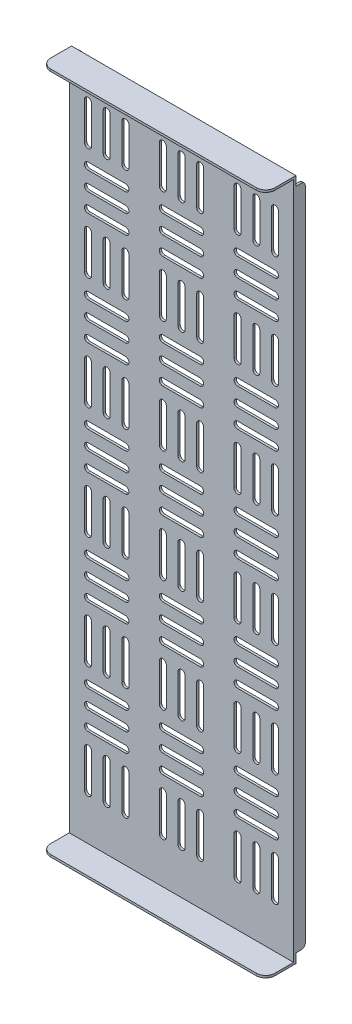
SolidWorks part; units mm, degrees
ref_plane "Front Plane" through (0, 0, 0) normal (0, 0, 1) x (1, 0, 0)
ref_plane "Top Plane" through (0, 0, 0) normal (0, 1, 0) x (1, 0, 0)
ref_plane "Right Plane" through (0, 0, 0) normal (1, 0, 0) x (0, 0, -1)
sketch "Sketch1" plane through (0, 0, 0) normal (0, 0, 1) x (1, 0, 0)
  line L0 (12.7, 438.15) -> (12.7, 412.75) construction
  line L1 (0, 0) -> (152.4, 0)
  line L2 (0, 0) -> (0, 463.55)
  line L3 (0, 463.55) -> (152.4, 463.55)
  line L4 (152.4, 0) -> (152.4, 463.55)
  line L5 (15.0812, 438.15) -> (15.0813, 412.75)
  line L6 (10.3188, 438.15) -> (10.3188, 412.75)
  line L7 (25.4, 438.15) -> (25.4, 412.75) construction
  line L8 (27.7812, 438.15) -> (27.7812, 412.75)
  line L9 (23.0188, 438.15) -> (23.0188, 412.75)
  line L10 (38.1, 438.15) -> (38.1, 412.75) construction
  line L11 (40.4812, 438.15) -> (40.4813, 412.75)
  line L12 (35.7188, 438.15) -> (35.7188, 412.75)
  line L13 (63.5, 438.15) -> (63.5, 412.75) construction
  line L14 (65.8813, 438.15) -> (65.8813, 412.75)
  line L15 (61.1187, 438.15) -> (61.1187, 412.75)
  line L16 (76.2, 438.15) -> (76.2, 412.75) construction
  line L17 (78.5812, 438.15) -> (78.5812, 412.75)
  line L18 (73.8188, 438.15) -> (73.8188, 412.75)
  line L19 (88.9, 438.15) -> (88.9, 412.75) construction
  line L20 (91.2812, 438.15) -> (91.2813, 412.75)
  line L21 (86.5188, 438.15) -> (86.5188, 412.75)
  line L22 (114.3, 438.15) -> (114.3, 412.75) construction
  line L23 (116.6813, 438.15) -> (116.6813, 412.75)
  line L24 (111.9188, 438.15) -> (111.9188, 412.75)
  line L25 (127, 438.15) -> (127, 412.75) construction
  line L26 (129.3812, 438.15) -> (129.3812, 412.75)
  line L27 (124.6188, 438.15) -> (124.6188, 412.75)
  line L28 (139.7, 438.15) -> (139.7, 412.75) construction
  line L29 (142.0812, 438.15) -> (142.0812, 412.75)
  line L30 (137.3187, 438.15) -> (137.3187, 412.75)
  line L31 (12.7, 400.05) -> (38.1, 400.05) construction
  line L32 (12.7, 402.4313) -> (38.1, 402.4313)
  line L33 (12.7, 397.6687) -> (38.1, 397.6687)
  line L34 (12.7, 387.35) -> (38.1, 387.35) construction
  line L35 (12.7, 389.7313) -> (38.1, 389.7313)
  line L36 (12.7, 384.9688) -> (38.1, 384.9688)
  line L37 (12.7, 374.65) -> (38.1, 374.65) construction
  line L38 (12.7, 377.0313) -> (38.1, 377.0313)
  line L39 (12.7, 372.2688) -> (38.1, 372.2688)
  line L40 (63.5, 400.05) -> (88.9, 400.05) construction
  line L41 (63.5, 402.4313) -> (88.9, 402.4313)
  line L42 (63.5, 397.6687) -> (88.9, 397.6687)
  line L43 (63.5, 387.35) -> (88.9, 387.35) construction
  line L44 (63.5, 389.7313) -> (88.9, 389.7313)
  line L45 (63.5, 384.9688) -> (88.9, 384.9688)
  line L46 (63.5, 374.65) -> (88.9, 374.65) construction
  line L47 (63.5, 377.0313) -> (88.9, 377.0313)
  line L48 (63.5, 372.2688) -> (88.9, 372.2688)
  line L49 (114.3, 400.05) -> (139.7, 400.05) construction
  line L50 (114.3, 402.4313) -> (139.7, 402.4313)
  line L51 (114.3, 397.6687) -> (139.7, 397.6687)
  line L52 (114.3, 387.35) -> (139.7, 387.35) construction
  line L53 (114.3, 389.7313) -> (139.7, 389.7313)
  line L54 (114.3, 384.9688) -> (139.7, 384.9688)
  line L55 (114.3, 374.65) -> (139.7, 374.65) construction
  line L56 (114.3, 377.0313) -> (139.7, 377.0313)
  line L57 (114.3, 372.2688) -> (139.7, 372.2688)
  line L58 (12.7, 361.95) -> (12.7, 336.55) construction
  line L59 (15.0813, 361.95) -> (15.0813, 336.55)
  line L60 (10.3188, 361.95) -> (10.3188, 336.55)
  line L61 (25.4, 361.95) -> (25.4, 336.55) construction
  line L62 (27.7813, 361.95) -> (27.7813, 336.55)
  line L63 (23.0188, 361.95) -> (23.0188, 336.55)
  line L64 (38.1, 361.95) -> (38.1, 336.55) construction
  line L65 (40.4813, 361.95) -> (40.4813, 336.55)
  line L66 (35.7188, 361.95) -> (35.7188, 336.55)
  line L67 (63.5, 361.95) -> (63.5, 336.55) construction
  line L68 (65.8813, 361.95) -> (65.8813, 336.55)
  line L69 (61.1188, 361.95) -> (61.1188, 336.55)
  line L70 (76.2, 361.95) -> (76.2, 336.55) construction
  line L71 (78.5813, 361.95) -> (78.5813, 336.55)
  line L72 (73.8188, 361.95) -> (73.8188, 336.55)
  line L73 (88.9, 361.95) -> (88.9, 336.55) construction
  line L74 (91.2813, 361.95) -> (91.2813, 336.55)
  line L75 (86.5188, 361.95) -> (86.5188, 336.55)
  line L76 (114.3, 361.95) -> (114.3, 336.55) construction
  line L77 (116.6813, 361.95) -> (116.6813, 336.55)
  line L78 (111.9188, 361.95) -> (111.9188, 336.55)
  line L79 (127, 361.95) -> (127, 336.55) construction
  line L80 (129.3813, 361.95) -> (129.3813, 336.55)
  line L81 (124.6188, 361.95) -> (124.6188, 336.55)
  line L82 (139.7, 361.95) -> (139.7, 336.55) construction
  line L83 (142.0813, 361.95) -> (142.0813, 336.55)
  line L84 (137.3188, 361.95) -> (137.3188, 336.55)
  line L85 (12.7, 323.85) -> (38.1, 323.85) construction
  line L86 (12.7, 326.2313) -> (38.1, 326.2313)
  line L87 (12.7, 321.4688) -> (38.1, 321.4688)
  line L88 (12.7, 311.15) -> (38.1, 311.15) construction
  line L89 (12.7, 313.5313) -> (38.1, 313.5313)
  line L90 (12.7, 308.7688) -> (38.1, 308.7688)
  line L91 (12.7, 298.45) -> (38.1, 298.45) construction
  line L92 (12.7, 300.8313) -> (38.1, 300.8313)
  line L93 (12.7, 296.0688) -> (38.1, 296.0688)
  line L94 (63.5, 323.85) -> (88.9, 323.85) construction
  line L95 (63.5, 326.2313) -> (88.9, 326.2313)
  line L96 (63.5, 321.4688) -> (88.9, 321.4688)
  line L97 (63.5, 311.15) -> (88.9, 311.15) construction
  line L98 (63.5, 313.5313) -> (88.9, 313.5313)
  line L99 (63.5, 308.7688) -> (88.9, 308.7688)
  line L100 (63.5, 298.45) -> (88.9, 298.45) construction
  line L101 (63.5, 300.8313) -> (88.9, 300.8313)
  line L102 (63.5, 296.0688) -> (88.9, 296.0688)
  line L103 (114.3, 323.85) -> (139.7, 323.85) construction
  line L104 (114.3, 326.2313) -> (139.7, 326.2313)
  line L105 (114.3, 321.4688) -> (139.7, 321.4688)
  line L106 (114.3, 311.15) -> (139.7, 311.15) construction
  line L107 (114.3, 313.5313) -> (139.7, 313.5313)
  line L108 (114.3, 308.7688) -> (139.7, 308.7688)
  line L109 (114.3, 298.45) -> (139.7, 298.45) construction
  line L110 (114.3, 300.8313) -> (139.7, 300.8313)
  line L111 (114.3, 296.0688) -> (139.7, 296.0688)
  line L112 (12.7, 285.75) -> (12.7, 260.35) construction
  line L113 (15.0813, 285.75) -> (15.0813, 260.35)
  line L114 (10.3188, 285.75) -> (10.3188, 260.35)
  line L115 (25.4, 285.75) -> (25.4, 260.35) construction
  line L116 (27.7813, 285.75) -> (27.7813, 260.35)
  line L117 (23.0188, 285.75) -> (23.0188, 260.35)
  line L118 (38.1, 285.75) -> (38.1, 260.35) construction
  line L119 (40.4813, 285.75) -> (40.4813, 260.35)
  line L120 (35.7188, 285.75) -> (35.7188, 260.35)
  line L121 (63.5, 285.75) -> (63.5, 260.35) construction
  line L122 (65.8813, 285.75) -> (65.8813, 260.35)
  line L123 (61.1188, 285.75) -> (61.1188, 260.35)
  line L124 (76.2, 285.75) -> (76.2, 260.35) construction
  line L125 (78.5813, 285.75) -> (78.5813, 260.35)
  line L126 (73.8188, 285.75) -> (73.8188, 260.35)
  line L127 (88.9, 285.75) -> (88.9, 260.35) construction
  line L128 (91.2813, 285.75) -> (91.2813, 260.35)
  line L129 (86.5188, 285.75) -> (86.5188, 260.35)
  line L130 (114.3, 285.75) -> (114.3, 260.35) construction
  line L131 (116.6813, 285.75) -> (116.6813, 260.35)
  line L132 (111.9188, 285.75) -> (111.9188, 260.35)
  line L133 (127, 285.75) -> (127, 260.35) construction
  line L134 (129.3813, 285.75) -> (129.3813, 260.35)
  line L135 (124.6188, 285.75) -> (124.6188, 260.35)
  line L136 (139.7, 285.75) -> (139.7, 260.35) construction
  line L137 (142.0813, 285.75) -> (142.0813, 260.35)
  line L138 (137.3188, 285.75) -> (137.3188, 260.35)
  line L139 (12.7, 247.65) -> (38.1, 247.65) construction
  line L140 (12.7, 250.0313) -> (38.1, 250.0313)
  line L141 (12.7, 245.2688) -> (38.1, 245.2688)
  line L142 (12.7, 234.95) -> (38.1, 234.95) construction
  line L143 (12.7, 237.3313) -> (38.1, 237.3313)
  line L144 (12.7, 232.5688) -> (38.1, 232.5688)
  line L145 (12.7, 222.25) -> (38.1, 222.25) construction
  line L146 (12.7, 224.6313) -> (38.1, 224.6313)
  line L147 (12.7, 219.8688) -> (38.1, 219.8688)
  line L148 (63.5, 247.65) -> (88.9, 247.65) construction
  line L149 (63.5, 250.0313) -> (88.9, 250.0313)
  line L150 (63.5, 245.2688) -> (88.9, 245.2688)
  line L151 (63.5, 234.95) -> (88.9, 234.95) construction
  line L152 (63.5, 237.3313) -> (88.9, 237.3313)
  line L153 (63.5, 232.5688) -> (88.9, 232.5688)
  line L154 (63.5, 222.25) -> (88.9, 222.25) construction
  line L155 (63.5, 224.6313) -> (88.9, 224.6313)
  line L156 (63.5, 219.8688) -> (88.9, 219.8688)
  line L157 (114.3, 247.65) -> (139.7, 247.65) construction
  line L158 (114.3, 250.0313) -> (139.7, 250.0313)
  line L159 (114.3, 245.2688) -> (139.7, 245.2688)
  line L160 (114.3, 234.95) -> (139.7, 234.95) construction
  line L161 (114.3, 237.3313) -> (139.7, 237.3313)
  line L162 (114.3, 232.5688) -> (139.7, 232.5688)
  line L163 (114.3, 222.25) -> (139.7, 222.25) construction
  line L164 (114.3, 224.6313) -> (139.7, 224.6313)
  line L165 (114.3, 219.8688) -> (139.7, 219.8688)
  line L166 (12.7, 209.55) -> (12.7, 184.15) construction
  line L167 (15.0813, 209.55) -> (15.0813, 184.15)
  line L168 (10.3188, 209.55) -> (10.3188, 184.15)
  line L169 (25.4, 209.55) -> (25.4, 184.15) construction
  line L170 (27.7813, 209.55) -> (27.7813, 184.15)
  line L171 (23.0188, 209.55) -> (23.0188, 184.15)
  line L172 (38.1, 209.55) -> (38.1, 184.15) construction
  line L173 (40.4813, 209.55) -> (40.4813, 184.15)
  line L174 (35.7188, 209.55) -> (35.7188, 184.15)
  line L175 (63.5, 209.55) -> (63.5, 184.15) construction
  line L176 (65.8813, 209.55) -> (65.8813, 184.15)
  line L177 (61.1188, 209.55) -> (61.1188, 184.15)
  line L178 (76.2, 209.55) -> (76.2, 184.15) construction
  line L179 (78.5813, 209.55) -> (78.5813, 184.15)
  line L180 (73.8188, 209.55) -> (73.8188, 184.15)
  line L181 (88.9, 209.55) -> (88.9, 184.15) construction
  line L182 (91.2813, 209.55) -> (91.2813, 184.15)
  line L183 (86.5188, 209.55) -> (86.5188, 184.15)
  line L184 (114.3, 209.55) -> (114.3, 184.15) construction
  line L185 (116.6813, 209.55) -> (116.6813, 184.15)
  line L186 (111.9188, 209.55) -> (111.9188, 184.15)
  line L187 (127, 209.55) -> (127, 184.15) construction
  line L188 (129.3813, 209.55) -> (129.3813, 184.15)
  line L189 (124.6188, 209.55) -> (124.6188, 184.15)
  line L190 (139.7, 209.55) -> (139.7, 184.15) construction
  line L191 (142.0813, 209.55) -> (142.0813, 184.15)
  line L192 (137.3188, 209.55) -> (137.3188, 184.15)
  line L193 (12.7, 171.45) -> (38.1, 171.45) construction
  line L194 (12.7, 173.8312) -> (38.1, 173.8312)
  line L195 (12.7, 169.0687) -> (38.1, 169.0687)
  line L196 (12.7, 158.75) -> (38.1, 158.75) construction
  line L197 (12.7, 161.1312) -> (38.1, 161.1312)
  line L198 (12.7, 156.3688) -> (38.1, 156.3688)
  line L199 (12.7, 146.05) -> (38.1, 146.05) construction
  line L200 (12.7, 148.4313) -> (38.1, 148.4313)
  line L201 (12.7, 143.6688) -> (38.1, 143.6688)
  line L202 (63.5, 171.45) -> (88.9, 171.45) construction
  line L203 (63.5, 173.8312) -> (88.9, 173.8312)
  line L204 (63.5, 169.0687) -> (88.9, 169.0687)
  line L205 (63.5, 158.75) -> (88.9, 158.75) construction
  line L206 (63.5, 161.1312) -> (88.9, 161.1312)
  line L207 (63.5, 156.3688) -> (88.9, 156.3688)
  line L208 (63.5, 146.05) -> (88.9, 146.05) construction
  line L209 (63.5, 148.4313) -> (88.9, 148.4313)
  line L210 (63.5, 143.6688) -> (88.9, 143.6688)
  line L211 (114.3, 171.45) -> (139.7, 171.45) construction
  line L212 (114.3, 173.8312) -> (139.7, 173.8312)
  line L213 (114.3, 169.0687) -> (139.7, 169.0687)
  line L214 (114.3, 158.75) -> (139.7, 158.75) construction
  line L215 (114.3, 161.1312) -> (139.7, 161.1312)
  line L216 (114.3, 156.3688) -> (139.7, 156.3688)
  line L217 (114.3, 146.05) -> (139.7, 146.05) construction
  line L218 (114.3, 148.4313) -> (139.7, 148.4313)
  line L219 (114.3, 143.6688) -> (139.7, 143.6688)
  line L220 (12.7, 133.35) -> (12.7, 107.95) construction
  line L221 (15.0813, 133.35) -> (15.0813, 107.95)
  line L222 (10.3187, 133.35) -> (10.3187, 107.95)
  line L223 (25.4, 133.35) -> (25.4, 107.95) construction
  line L224 (27.7813, 133.35) -> (27.7813, 107.95)
  line L225 (23.0187, 133.35) -> (23.0187, 107.95)
  line L226 (38.1, 133.35) -> (38.1, 107.95) construction
  line L227 (40.4813, 133.35) -> (40.4813, 107.95)
  line L228 (35.7187, 133.35) -> (35.7187, 107.95)
  line L229 (63.5, 133.35) -> (63.5, 107.95) construction
  line L230 (65.8813, 133.35) -> (65.8813, 107.95)
  line L231 (61.1187, 133.35) -> (61.1187, 107.95)
  line L232 (76.2, 133.35) -> (76.2, 107.95) construction
  line L233 (78.5813, 133.35) -> (78.5813, 107.95)
  line L234 (73.8187, 133.35) -> (73.8187, 107.95)
  line L235 (88.9, 133.35) -> (88.9, 107.95) construction
  line L236 (91.2813, 133.35) -> (91.2813, 107.95)
  line L237 (86.5187, 133.35) -> (86.5187, 107.95)
  line L238 (114.3, 133.35) -> (114.3, 107.95) construction
  line L239 (116.6813, 133.35) -> (116.6813, 107.95)
  line L240 (111.9187, 133.35) -> (111.9187, 107.95)
  line L241 (127, 133.35) -> (127, 107.95) construction
  line L242 (129.3813, 133.35) -> (129.3813, 107.95)
  line L243 (124.6187, 133.35) -> (124.6187, 107.95)
  line L244 (139.7, 133.35) -> (139.7, 107.95) construction
  line L245 (142.0813, 133.35) -> (142.0813, 107.95)
  line L246 (137.3187, 133.35) -> (137.3187, 107.95)
  line L247 (12.7, 95.25) -> (38.1, 95.25) construction
  line L248 (12.7, 97.6313) -> (38.1, 97.6313)
  line L249 (12.7, 92.8688) -> (38.1, 92.8688)
  line L250 (12.7, 82.55) -> (38.1, 82.55) construction
  line L251 (12.7, 84.9313) -> (38.1, 84.9313)
  line L252 (12.7, 80.1688) -> (38.1, 80.1688)
  line L253 (12.7, 69.85) -> (38.1, 69.85) construction
  line L254 (12.7, 72.2313) -> (38.1, 72.2313)
  line L255 (12.7, 67.4688) -> (38.1, 67.4688)
  line L256 (63.5, 95.25) -> (88.9, 95.25) construction
  line L257 (63.5, 97.6313) -> (88.9, 97.6313)
  line L258 (63.5, 92.8688) -> (88.9, 92.8688)
  line L259 (63.5, 82.55) -> (88.9, 82.55) construction
  line L260 (63.5, 84.9313) -> (88.9, 84.9313)
  line L261 (63.5, 80.1688) -> (88.9, 80.1688)
  line L262 (63.5, 69.85) -> (88.9, 69.85) construction
  line L263 (63.5, 72.2313) -> (88.9, 72.2313)
  line L264 (63.5, 67.4688) -> (88.9, 67.4688)
  line L265 (114.3, 95.25) -> (139.7, 95.25) construction
  line L266 (114.3, 97.6313) -> (139.7, 97.6313)
  line L267 (114.3, 92.8688) -> (139.7, 92.8688)
  line L268 (114.3, 82.55) -> (139.7, 82.55) construction
  line L269 (114.3, 84.9313) -> (139.7, 84.9313)
  line L270 (114.3, 80.1688) -> (139.7, 80.1688)
  line L271 (114.3, 69.85) -> (139.7, 69.85) construction
  line L272 (114.3, 72.2313) -> (139.7, 72.2313)
  line L273 (114.3, 67.4688) -> (139.7, 67.4688)
  line L274 (12.7, 57.15) -> (12.7, 31.75) construction
  line L275 (15.0813, 57.15) -> (15.0813, 31.75)
  line L276 (10.3187, 57.15) -> (10.3187, 31.75)
  line L277 (25.4, 57.15) -> (25.4, 31.75) construction
  line L278 (27.7813, 57.15) -> (27.7813, 31.75)
  line L279 (23.0187, 57.15) -> (23.0187, 31.75)
  line L280 (38.1, 57.15) -> (38.1, 31.75) construction
  line L281 (40.4813, 57.15) -> (40.4813, 31.75)
  line L282 (35.7187, 57.15) -> (35.7187, 31.75)
  line L283 (63.5, 57.15) -> (63.5, 31.75) construction
  line L284 (65.8813, 57.15) -> (65.8813, 31.75)
  line L285 (61.1187, 57.15) -> (61.1187, 31.75)
  line L286 (76.2, 57.15) -> (76.2, 31.75) construction
  line L287 (78.5813, 57.15) -> (78.5813, 31.75)
  line L288 (73.8187, 57.15) -> (73.8187, 31.75)
  line L289 (88.9, 57.15) -> (88.9, 31.75) construction
  line L290 (91.2813, 57.15) -> (91.2813, 31.75)
  line L291 (86.5187, 57.15) -> (86.5187, 31.75)
  line L292 (114.3, 57.15) -> (114.3, 31.75) construction
  line L293 (116.6813, 57.15) -> (116.6813, 31.75)
  line L294 (111.9187, 57.15) -> (111.9187, 31.75)
  line L295 (127, 57.15) -> (127, 31.75) construction
  line L296 (129.3813, 57.15) -> (129.3813, 31.75)
  line L297 (124.6187, 57.15) -> (124.6187, 31.75)
  line L298 (139.7, 57.15) -> (139.7, 31.75) construction
  line L299 (142.0813, 57.15) -> (142.0813, 31.75)
  line L300 (137.3187, 57.15) -> (137.3187, 31.75)
  line L331 (12.7, 6.35) -> (38.1, 6.35) construction
  line L332 (12.7, 8.7313) -> (38.1, 8.7313)
  line L333 (12.7, 3.9688) -> (38.1, 3.9688)
  line L334 (12.7, -6.35) -> (38.1, -6.35) construction
  line L335 (12.7, -3.9687) -> (38.1, -3.9687)
  line L336 (12.7, -8.7312) -> (38.1, -8.7312)
  line L337 (63.5, 19.05) -> (88.9, 19.05) construction
  line L338 (63.5, 21.4313) -> (88.9, 21.4313)
  line L339 (63.5, 16.6688) -> (88.9, 16.6688)
  line L340 (63.5, 6.35) -> (88.9, 6.35) construction
  line L341 (63.5, 8.7313) -> (88.9, 8.7313)
  line L342 (63.5, 3.9688) -> (88.9, 3.9688)
  line L343 (63.5, -6.35) -> (88.9, -6.35) construction
  line L344 (63.5, -3.9687) -> (88.9, -3.9687)
  line L345 (63.5, -8.7312) -> (88.9, -8.7312)
  line L346 (114.3, 19.05) -> (139.7, 19.05) construction
  line L347 (114.3, 21.4313) -> (139.7, 21.4313)
  line L348 (114.3, 16.6688) -> (139.7, 16.6688)
  line L349 (114.3, 6.35) -> (139.7, 6.35) construction
  line L350 (114.3, 8.7313) -> (139.7, 8.7313)
  line L351 (114.3, 3.9688) -> (139.7, 3.9688)
  line L352 (114.3, -6.35) -> (139.7, -6.35) construction
  line L353 (114.3, -3.9687) -> (139.7, -3.9687)
  line L354 (114.3, -8.7312) -> (139.7, -8.7312)
  line L355 (12.7, 19.05) -> (38.1, 19.05) construction
  line L356 (12.7, 21.4313) -> (38.1, 21.4313)
  line L357 (12.7, 16.6688) -> (38.1, 16.6688)
  line L358 (12.7, 6.35) -> (38.1, 6.35) construction
  line L359 (12.7, 8.7313) -> (38.1, 8.7313)
  line L360 (12.7, 3.9688) -> (38.1, 3.9688)
  line L361 (12.7, -6.35) -> (38.1, -6.35) construction
  line L362 (12.7, -3.9687) -> (38.1, -3.9687)
  line L363 (12.7, -8.7312) -> (38.1, -8.7312)
  line L364 (63.5, 19.05) -> (88.9, 19.05) construction
  line L365 (63.5, 21.4313) -> (88.9, 21.4313)
  line L366 (63.5, 16.6688) -> (88.9, 16.6688)
  line L367 (63.5, 6.35) -> (88.9, 6.35) construction
  line L368 (63.5, 8.7313) -> (88.9, 8.7313)
  line L369 (63.5, 3.9688) -> (88.9, 3.9688)
  line L370 (63.5, -6.35) -> (88.9, -6.35) construction
  line L371 (63.5, -3.9687) -> (88.9, -3.9687)
  line L372 (63.5, -8.7312) -> (88.9, -8.7312)
  line L373 (114.3, 19.05) -> (139.7, 19.05) construction
  line L374 (114.3, 21.4313) -> (139.7, 21.4313)
  line L375 (114.3, 16.6688) -> (139.7, 16.6688)
  line L376 (114.3, 6.35) -> (139.7, 6.35) construction
  line L377 (114.3, 8.7313) -> (139.7, 8.7313)
  line L378 (114.3, 3.9688) -> (139.7, 3.9688)
  line L379 (114.3, -6.35) -> (139.7, -6.35) construction
  line L380 (114.3, -3.9687) -> (139.7, -3.9687)
  line L381 (114.3, -8.7312) -> (139.7, -8.7312)
  line L382 (12.7, 19.05) -> (38.1, 19.05) construction
  line L383 (12.7, 21.4313) -> (38.1, 21.4313)
  line L384 (12.7, 16.6688) -> (38.1, 16.6688)
  arc A0 (15.0812, 438.15) -> (10.3188, 438.15) centre (12.7, 438.15) ccw
  arc A1 (10.3188, 412.75) -> (15.0813, 412.75) centre (12.7, 412.75) ccw
  arc A2 (27.7812, 438.15) -> (23.0188, 438.15) centre (25.4, 438.15) ccw
  arc A3 (23.0188, 412.75) -> (27.7812, 412.75) centre (25.4, 412.75) ccw
  arc A4 (40.4812, 438.15) -> (35.7188, 438.15) centre (38.1, 438.15) ccw
  arc A5 (35.7188, 412.75) -> (40.4813, 412.75) centre (38.1, 412.75) ccw
  arc A6 (65.8813, 438.15) -> (61.1187, 438.15) centre (63.5, 438.15) ccw
  arc A7 (61.1187, 412.75) -> (65.8813, 412.75) centre (63.5, 412.75) ccw
  arc A8 (78.5812, 438.15) -> (73.8188, 438.15) centre (76.2, 438.15) ccw
  arc A9 (73.8188, 412.75) -> (78.5812, 412.75) centre (76.2, 412.75) ccw
  arc A10 (91.2812, 438.15) -> (86.5188, 438.15) centre (88.9, 438.15) ccw
  arc A11 (86.5188, 412.75) -> (91.2813, 412.75) centre (88.9, 412.75) ccw
  arc A12 (116.6813, 438.15) -> (111.9188, 438.15) centre (114.3, 438.15) ccw
  arc A13 (111.9188, 412.75) -> (116.6813, 412.75) centre (114.3, 412.75) ccw
  arc A14 (129.3812, 438.15) -> (124.6188, 438.15) centre (127, 438.15) ccw
  arc A15 (124.6188, 412.75) -> (129.3812, 412.75) centre (127, 412.75) ccw
  arc A16 (142.0812, 438.15) -> (137.3187, 438.15) centre (139.7, 438.15) ccw
  arc A17 (137.3187, 412.75) -> (142.0812, 412.75) centre (139.7, 412.75) ccw
  arc A18 (12.7, 402.4313) -> (12.7, 397.6687) centre (12.7, 400.05) ccw
  arc A19 (38.1, 397.6687) -> (38.1, 402.4313) centre (38.1, 400.05) ccw
  arc A20 (12.7, 389.7313) -> (12.7, 384.9688) centre (12.7, 387.35) ccw
  arc A21 (38.1, 384.9688) -> (38.1, 389.7313) centre (38.1, 387.35) ccw
  arc A22 (12.7, 377.0313) -> (12.7, 372.2688) centre (12.7, 374.65) ccw
  arc A23 (38.1, 372.2688) -> (38.1, 377.0313) centre (38.1, 374.65) ccw
  arc A24 (63.5, 402.4313) -> (63.5, 397.6687) centre (63.5, 400.05) ccw
  arc A25 (88.9, 397.6687) -> (88.9, 402.4313) centre (88.9, 400.05) ccw
  arc A26 (63.5, 389.7313) -> (63.5, 384.9688) centre (63.5, 387.35) ccw
  arc A27 (88.9, 384.9688) -> (88.9, 389.7313) centre (88.9, 387.35) ccw
  arc A28 (63.5, 377.0313) -> (63.5, 372.2688) centre (63.5, 374.65) ccw
  arc A29 (88.9, 372.2688) -> (88.9, 377.0313) centre (88.9, 374.65) ccw
  arc A30 (114.3, 402.4313) -> (114.3, 397.6687) centre (114.3, 400.05) ccw
  arc A31 (139.7, 397.6687) -> (139.7, 402.4313) centre (139.7, 400.05) ccw
  arc A32 (114.3, 389.7313) -> (114.3, 384.9688) centre (114.3, 387.35) ccw
  arc A33 (139.7, 384.9688) -> (139.7, 389.7313) centre (139.7, 387.35) ccw
  arc A34 (114.3, 377.0313) -> (114.3, 372.2688) centre (114.3, 374.65) ccw
  arc A35 (139.7, 372.2688) -> (139.7, 377.0313) centre (139.7, 374.65) ccw
  arc A36 (15.0813, 361.95) -> (10.3188, 361.95) centre (12.7, 361.95) ccw
  arc A37 (10.3188, 336.55) -> (15.0813, 336.55) centre (12.7, 336.55) ccw
  arc A38 (27.7813, 361.95) -> (23.0188, 361.95) centre (25.4, 361.95) ccw
  arc A39 (23.0188, 336.55) -> (27.7813, 336.55) centre (25.4, 336.55) ccw
  arc A40 (40.4813, 361.95) -> (35.7188, 361.95) centre (38.1, 361.95) ccw
  arc A41 (35.7188, 336.55) -> (40.4813, 336.55) centre (38.1, 336.55) ccw
  arc A42 (65.8813, 361.95) -> (61.1188, 361.95) centre (63.5, 361.95) ccw
  arc A43 (61.1188, 336.55) -> (65.8813, 336.55) centre (63.5, 336.55) ccw
  arc A44 (78.5813, 361.95) -> (73.8188, 361.95) centre (76.2, 361.95) ccw
  arc A45 (73.8188, 336.55) -> (78.5813, 336.55) centre (76.2, 336.55) ccw
  arc A46 (91.2813, 361.95) -> (86.5188, 361.95) centre (88.9, 361.95) ccw
  arc A47 (86.5188, 336.55) -> (91.2813, 336.55) centre (88.9, 336.55) ccw
  arc A48 (116.6813, 361.95) -> (111.9188, 361.95) centre (114.3, 361.95) ccw
  arc A49 (111.9188, 336.55) -> (116.6813, 336.55) centre (114.3, 336.55) ccw
  arc A50 (129.3813, 361.95) -> (124.6188, 361.95) centre (127, 361.95) ccw
  arc A51 (124.6188, 336.55) -> (129.3813, 336.55) centre (127, 336.55) ccw
  arc A52 (142.0813, 361.95) -> (137.3188, 361.95) centre (139.7, 361.95) ccw
  arc A53 (137.3188, 336.55) -> (142.0813, 336.55) centre (139.7, 336.55) ccw
  arc A54 (12.7, 326.2313) -> (12.7, 321.4688) centre (12.7, 323.85) ccw
  arc A55 (38.1, 321.4688) -> (38.1, 326.2313) centre (38.1, 323.85) ccw
  arc A56 (12.7, 313.5313) -> (12.7, 308.7688) centre (12.7, 311.15) ccw
  arc A57 (38.1, 308.7688) -> (38.1, 313.5313) centre (38.1, 311.15) ccw
  arc A58 (12.7, 300.8313) -> (12.7, 296.0688) centre (12.7, 298.45) ccw
  arc A59 (38.1, 296.0688) -> (38.1, 300.8313) centre (38.1, 298.45) ccw
  arc A60 (63.5, 326.2313) -> (63.5, 321.4688) centre (63.5, 323.85) ccw
  arc A61 (88.9, 321.4688) -> (88.9, 326.2313) centre (88.9, 323.85) ccw
  arc A62 (63.5, 313.5313) -> (63.5, 308.7688) centre (63.5, 311.15) ccw
  arc A63 (88.9, 308.7688) -> (88.9, 313.5313) centre (88.9, 311.15) ccw
  arc A64 (63.5, 300.8313) -> (63.5, 296.0688) centre (63.5, 298.45) ccw
  arc A65 (88.9, 296.0688) -> (88.9, 300.8313) centre (88.9, 298.45) ccw
  arc A66 (114.3, 326.2313) -> (114.3, 321.4688) centre (114.3, 323.85) ccw
  arc A67 (139.7, 321.4688) -> (139.7, 326.2313) centre (139.7, 323.85) ccw
  arc A68 (114.3, 313.5313) -> (114.3, 308.7688) centre (114.3, 311.15) ccw
  arc A69 (139.7, 308.7688) -> (139.7, 313.5313) centre (139.7, 311.15) ccw
  arc A70 (114.3, 300.8313) -> (114.3, 296.0688) centre (114.3, 298.45) ccw
  arc A71 (139.7, 296.0688) -> (139.7, 300.8313) centre (139.7, 298.45) ccw
  arc A72 (15.0813, 285.75) -> (10.3188, 285.75) centre (12.7, 285.75) ccw
  arc A73 (10.3188, 260.35) -> (15.0813, 260.35) centre (12.7, 260.35) ccw
  arc A74 (27.7813, 285.75) -> (23.0188, 285.75) centre (25.4, 285.75) ccw
  arc A75 (23.0188, 260.35) -> (27.7813, 260.35) centre (25.4, 260.35) ccw
  arc A76 (40.4813, 285.75) -> (35.7188, 285.75) centre (38.1, 285.75) ccw
  arc A77 (35.7188, 260.35) -> (40.4813, 260.35) centre (38.1, 260.35) ccw
  arc A78 (65.8813, 285.75) -> (61.1188, 285.75) centre (63.5, 285.75) ccw
  arc A79 (61.1188, 260.35) -> (65.8813, 260.35) centre (63.5, 260.35) ccw
  arc A80 (78.5813, 285.75) -> (73.8188, 285.75) centre (76.2, 285.75) ccw
  arc A81 (73.8188, 260.35) -> (78.5813, 260.35) centre (76.2, 260.35) ccw
  arc A82 (91.2813, 285.75) -> (86.5188, 285.75) centre (88.9, 285.75) ccw
  arc A83 (86.5188, 260.35) -> (91.2813, 260.35) centre (88.9, 260.35) ccw
  arc A84 (116.6813, 285.75) -> (111.9188, 285.75) centre (114.3, 285.75) ccw
  arc A85 (111.9188, 260.35) -> (116.6813, 260.35) centre (114.3, 260.35) ccw
  arc A86 (129.3813, 285.75) -> (124.6188, 285.75) centre (127, 285.75) ccw
  arc A87 (124.6188, 260.35) -> (129.3813, 260.35) centre (127, 260.35) ccw
  arc A88 (142.0813, 285.75) -> (137.3188, 285.75) centre (139.7, 285.75) ccw
  arc A89 (137.3188, 260.35) -> (142.0813, 260.35) centre (139.7, 260.35) ccw
  arc A90 (12.7, 250.0313) -> (12.7, 245.2688) centre (12.7, 247.65) ccw
  arc A91 (38.1, 245.2688) -> (38.1, 250.0313) centre (38.1, 247.65) ccw
  arc A92 (12.7, 237.3313) -> (12.7, 232.5688) centre (12.7, 234.95) ccw
  arc A93 (38.1, 232.5688) -> (38.1, 237.3313) centre (38.1, 234.95) ccw
  arc A94 (12.7, 224.6313) -> (12.7, 219.8688) centre (12.7, 222.25) ccw
  arc A95 (38.1, 219.8688) -> (38.1, 224.6313) centre (38.1, 222.25) ccw
  arc A96 (63.5, 250.0313) -> (63.5, 245.2688) centre (63.5, 247.65) ccw
  arc A97 (88.9, 245.2688) -> (88.9, 250.0313) centre (88.9, 247.65) ccw
  arc A98 (63.5, 237.3313) -> (63.5, 232.5688) centre (63.5, 234.95) ccw
  arc A99 (88.9, 232.5688) -> (88.9, 237.3313) centre (88.9, 234.95) ccw
  arc A100 (63.5, 224.6313) -> (63.5, 219.8688) centre (63.5, 222.25) ccw
  arc A101 (88.9, 219.8688) -> (88.9, 224.6313) centre (88.9, 222.25) ccw
  arc A102 (114.3, 250.0313) -> (114.3, 245.2688) centre (114.3, 247.65) ccw
  arc A103 (139.7, 245.2688) -> (139.7, 250.0313) centre (139.7, 247.65) ccw
  arc A104 (114.3, 237.3313) -> (114.3, 232.5688) centre (114.3, 234.95) ccw
  arc A105 (139.7, 232.5688) -> (139.7, 237.3313) centre (139.7, 234.95) ccw
  arc A106 (114.3, 224.6313) -> (114.3, 219.8688) centre (114.3, 222.25) ccw
  arc A107 (139.7, 219.8688) -> (139.7, 224.6313) centre (139.7, 222.25) ccw
  arc A108 (15.0813, 209.55) -> (10.3188, 209.55) centre (12.7, 209.55) ccw
  arc A109 (10.3188, 184.15) -> (15.0813, 184.15) centre (12.7, 184.15) ccw
  arc A110 (27.7813, 209.55) -> (23.0188, 209.55) centre (25.4, 209.55) ccw
  arc A111 (23.0188, 184.15) -> (27.7813, 184.15) centre (25.4, 184.15) ccw
  arc A112 (40.4813, 209.55) -> (35.7188, 209.55) centre (38.1, 209.55) ccw
  arc A113 (35.7188, 184.15) -> (40.4813, 184.15) centre (38.1, 184.15) ccw
  arc A114 (65.8813, 209.55) -> (61.1188, 209.55) centre (63.5, 209.55) ccw
  arc A115 (61.1188, 184.15) -> (65.8813, 184.15) centre (63.5, 184.15) ccw
  arc A116 (78.5813, 209.55) -> (73.8188, 209.55) centre (76.2, 209.55) ccw
  arc A117 (73.8188, 184.15) -> (78.5813, 184.15) centre (76.2, 184.15) ccw
  arc A118 (91.2813, 209.55) -> (86.5188, 209.55) centre (88.9, 209.55) ccw
  arc A119 (86.5188, 184.15) -> (91.2813, 184.15) centre (88.9, 184.15) ccw
  arc A120 (116.6813, 209.55) -> (111.9188, 209.55) centre (114.3, 209.55) ccw
  arc A121 (111.9188, 184.15) -> (116.6813, 184.15) centre (114.3, 184.15) ccw
  arc A122 (129.3813, 209.55) -> (124.6188, 209.55) centre (127, 209.55) ccw
  arc A123 (124.6188, 184.15) -> (129.3813, 184.15) centre (127, 184.15) ccw
  arc A124 (142.0813, 209.55) -> (137.3188, 209.55) centre (139.7, 209.55) ccw
  arc A125 (137.3188, 184.15) -> (142.0813, 184.15) centre (139.7, 184.15) ccw
  arc A126 (12.7, 173.8312) -> (12.7, 169.0687) centre (12.7, 171.45) ccw
  arc A127 (38.1, 169.0687) -> (38.1, 173.8312) centre (38.1, 171.45) ccw
  arc A128 (12.7, 161.1312) -> (12.7, 156.3688) centre (12.7, 158.75) ccw
  arc A129 (38.1, 156.3688) -> (38.1, 161.1312) centre (38.1, 158.75) ccw
  arc A130 (12.7, 148.4313) -> (12.7, 143.6688) centre (12.7, 146.05) ccw
  arc A131 (38.1, 143.6688) -> (38.1, 148.4313) centre (38.1, 146.05) ccw
  arc A132 (63.5, 173.8312) -> (63.5, 169.0687) centre (63.5, 171.45) ccw
  arc A133 (88.9, 169.0687) -> (88.9, 173.8312) centre (88.9, 171.45) ccw
  arc A134 (63.5, 161.1312) -> (63.5, 156.3688) centre (63.5, 158.75) ccw
  arc A135 (88.9, 156.3688) -> (88.9, 161.1312) centre (88.9, 158.75) ccw
  arc A136 (63.5, 148.4313) -> (63.5, 143.6688) centre (63.5, 146.05) ccw
  arc A137 (88.9, 143.6688) -> (88.9, 148.4313) centre (88.9, 146.05) ccw
  arc A138 (114.3, 173.8312) -> (114.3, 169.0687) centre (114.3, 171.45) ccw
  arc A139 (139.7, 169.0687) -> (139.7, 173.8312) centre (139.7, 171.45) ccw
  arc A140 (114.3, 161.1312) -> (114.3, 156.3688) centre (114.3, 158.75) ccw
  arc A141 (139.7, 156.3688) -> (139.7, 161.1312) centre (139.7, 158.75) ccw
  arc A142 (114.3, 148.4313) -> (114.3, 143.6688) centre (114.3, 146.05) ccw
  arc A143 (139.7, 143.6688) -> (139.7, 148.4313) centre (139.7, 146.05) ccw
  arc A144 (15.0813, 133.35) -> (10.3187, 133.35) centre (12.7, 133.35) ccw
  arc A145 (10.3187, 107.95) -> (15.0813, 107.95) centre (12.7, 107.95) ccw
  arc A146 (27.7813, 133.35) -> (23.0187, 133.35) centre (25.4, 133.35) ccw
  arc A147 (23.0187, 107.95) -> (27.7813, 107.95) centre (25.4, 107.95) ccw
  arc A148 (40.4813, 133.35) -> (35.7187, 133.35) centre (38.1, 133.35) ccw
  arc A149 (35.7187, 107.95) -> (40.4813, 107.95) centre (38.1, 107.95) ccw
  arc A150 (65.8813, 133.35) -> (61.1187, 133.35) centre (63.5, 133.35) ccw
  arc A151 (61.1187, 107.95) -> (65.8813, 107.95) centre (63.5, 107.95) ccw
  arc A152 (78.5813, 133.35) -> (73.8187, 133.35) centre (76.2, 133.35) ccw
  arc A153 (73.8187, 107.95) -> (78.5813, 107.95) centre (76.2, 107.95) ccw
  arc A154 (91.2813, 133.35) -> (86.5187, 133.35) centre (88.9, 133.35) ccw
  arc A155 (86.5187, 107.95) -> (91.2813, 107.95) centre (88.9, 107.95) ccw
  arc A156 (116.6813, 133.35) -> (111.9187, 133.35) centre (114.3, 133.35) ccw
  arc A157 (111.9187, 107.95) -> (116.6813, 107.95) centre (114.3, 107.95) ccw
  arc A158 (129.3813, 133.35) -> (124.6187, 133.35) centre (127, 133.35) ccw
  arc A159 (124.6187, 107.95) -> (129.3813, 107.95) centre (127, 107.95) ccw
  arc A160 (142.0813, 133.35) -> (137.3187, 133.35) centre (139.7, 133.35) ccw
  arc A161 (137.3187, 107.95) -> (142.0813, 107.95) centre (139.7, 107.95) ccw
  arc A162 (12.7, 97.6313) -> (12.7, 92.8688) centre (12.7, 95.25) ccw
  arc A163 (38.1, 92.8688) -> (38.1, 97.6313) centre (38.1, 95.25) ccw
  arc A164 (12.7, 84.9313) -> (12.7, 80.1688) centre (12.7, 82.55) ccw
  arc A165 (38.1, 80.1688) -> (38.1, 84.9313) centre (38.1, 82.55) ccw
  arc A166 (12.7, 72.2313) -> (12.7, 67.4688) centre (12.7, 69.85) ccw
  arc A167 (38.1, 67.4688) -> (38.1, 72.2313) centre (38.1, 69.85) ccw
  arc A168 (63.5, 97.6313) -> (63.5, 92.8688) centre (63.5, 95.25) ccw
  arc A169 (88.9, 92.8688) -> (88.9, 97.6313) centre (88.9, 95.25) ccw
  arc A170 (63.5, 84.9313) -> (63.5, 80.1688) centre (63.5, 82.55) ccw
  arc A171 (88.9, 80.1688) -> (88.9, 84.9313) centre (88.9, 82.55) ccw
  arc A172 (63.5, 72.2313) -> (63.5, 67.4688) centre (63.5, 69.85) ccw
  arc A173 (88.9, 67.4688) -> (88.9, 72.2313) centre (88.9, 69.85) ccw
  arc A174 (114.3, 97.6313) -> (114.3, 92.8688) centre (114.3, 95.25) ccw
  arc A175 (139.7, 92.8688) -> (139.7, 97.6313) centre (139.7, 95.25) ccw
  arc A176 (114.3, 84.9313) -> (114.3, 80.1688) centre (114.3, 82.55) ccw
  arc A177 (139.7, 80.1688) -> (139.7, 84.9313) centre (139.7, 82.55) ccw
  arc A178 (114.3, 72.2313) -> (114.3, 67.4688) centre (114.3, 69.85) ccw
  arc A179 (139.7, 67.4688) -> (139.7, 72.2313) centre (139.7, 69.85) ccw
  arc A180 (15.0813, 57.15) -> (10.3187, 57.15) centre (12.7, 57.15) ccw
  arc A181 (10.3187, 31.75) -> (15.0813, 31.75) centre (12.7, 31.75) ccw
  arc A182 (27.7813, 57.15) -> (23.0187, 57.15) centre (25.4, 57.15) ccw
  arc A183 (23.0187, 31.75) -> (27.7813, 31.75) centre (25.4, 31.75) ccw
  arc A184 (40.4813, 57.15) -> (35.7187, 57.15) centre (38.1, 57.15) ccw
  arc A185 (35.7187, 31.75) -> (40.4813, 31.75) centre (38.1, 31.75) ccw
  arc A186 (65.8813, 57.15) -> (61.1187, 57.15) centre (63.5, 57.15) ccw
  arc A187 (61.1187, 31.75) -> (65.8813, 31.75) centre (63.5, 31.75) ccw
  arc A188 (78.5813, 57.15) -> (73.8187, 57.15) centre (76.2, 57.15) ccw
  arc A189 (73.8187, 31.75) -> (78.5813, 31.75) centre (76.2, 31.75) ccw
  arc A190 (91.2813, 57.15) -> (86.5187, 57.15) centre (88.9, 57.15) ccw
  arc A191 (86.5187, 31.75) -> (91.2813, 31.75) centre (88.9, 31.75) ccw
  arc A192 (116.6813, 57.15) -> (111.9187, 57.15) centre (114.3, 57.15) ccw
  arc A193 (111.9187, 31.75) -> (116.6813, 31.75) centre (114.3, 31.75) ccw
  arc A194 (129.3813, 57.15) -> (124.6187, 57.15) centre (127, 57.15) ccw
  arc A195 (124.6187, 31.75) -> (129.3813, 31.75) centre (127, 31.75) ccw
  arc A196 (142.0813, 57.15) -> (137.3187, 57.15) centre (139.7, 57.15) ccw
  arc A197 (137.3187, 31.75) -> (142.0813, 31.75) centre (139.7, 31.75) ccw
  arc A236 (12.7, 8.7313) -> (12.7, 3.9688) centre (12.7, 6.35) ccw
  arc A237 (38.1, 3.9688) -> (38.1, 8.7313) centre (38.1, 6.35) ccw
  arc A238 (12.7, -3.9687) -> (12.7, -8.7312) centre (12.7, -6.35) ccw
  arc A239 (38.1, -8.7312) -> (38.1, -3.9687) centre (38.1, -6.35) ccw
  arc A240 (63.5, 21.4313) -> (63.5, 16.6688) centre (63.5, 19.05) ccw
  arc A241 (88.9, 16.6688) -> (88.9, 21.4313) centre (88.9, 19.05) ccw
  arc A242 (63.5, 8.7313) -> (63.5, 3.9688) centre (63.5, 6.35) ccw
  arc A243 (88.9, 3.9688) -> (88.9, 8.7313) centre (88.9, 6.35) ccw
  arc A244 (63.5, -3.9687) -> (63.5, -8.7312) centre (63.5, -6.35) ccw
  arc A245 (88.9, -8.7312) -> (88.9, -3.9687) centre (88.9, -6.35) ccw
  arc A246 (114.3, 21.4313) -> (114.3, 16.6688) centre (114.3, 19.05) ccw
  arc A247 (139.7, 16.6688) -> (139.7, 21.4313) centre (139.7, 19.05) ccw
  arc A248 (114.3, 8.7313) -> (114.3, 3.9688) centre (114.3, 6.35) ccw
  arc A249 (139.7, 3.9688) -> (139.7, 8.7313) centre (139.7, 6.35) ccw
  arc A250 (114.3, -3.9687) -> (114.3, -8.7312) centre (114.3, -6.35) ccw
  arc A251 (139.7, -8.7312) -> (139.7, -3.9687) centre (139.7, -6.35) ccw
  arc A252 (12.7, 21.4313) -> (12.7, 16.6688) centre (12.7, 19.05) ccw
  arc A253 (38.1, 16.6688) -> (38.1, 21.4313) centre (38.1, 19.05) ccw
  point P7 (12.7, 425.45)
  point P15 (25.4, 425.45)
  point P22 (38.1, 425.45)
  point P29 (63.5, 425.45)
  point P36 (76.2, 425.45)
  point P43 (88.9, 425.45)
  point P50 (114.3, 425.45)
  point P57 (127, 425.45)
  point P64 (139.7, 425.45)
  point P70 (25.4, 400.05)
  point P78 (25.4, 387.35)
  point P85 (25.4, 374.65)
  point P92 (76.2, 400.05)
  point P99 (76.2, 387.35)
  point P106 (76.2, 374.65)
  point P113 (127, 400.05)
  point P120 (127, 387.35)
  point P127 (127, 374.65)
  point P134 (12.7, 349.25)
  point P142 (25.4, 349.25)
  point P149 (38.1, 349.25)
  point P156 (63.5, 349.25)
  point P163 (76.2, 349.25)
  point P170 (88.9, 349.25)
  point P177 (114.3, 349.25)
  point P184 (127, 349.25)
  point P191 (139.7, 349.25)
  point P197 (25.4, 323.85)
  point P204 (25.4, 311.15)
  point P211 (25.4, 298.45)
  point P218 (76.2, 323.85)
  point P225 (76.2, 311.15)
  point P232 (76.2, 298.45)
  point P239 (127, 323.85)
  point P246 (127, 311.15)
  point P253 (127, 298.45)
  point P260 (12.7, 273.05)
  point P268 (25.4, 273.05)
  point P275 (38.1, 273.05)
  point P282 (63.5, 273.05)
  point P289 (76.2, 273.05)
  point P296 (88.9, 273.05)
  point P303 (114.3, 273.05)
  point P310 (127, 273.05)
  point P317 (139.7, 273.05)
  point P323 (25.4, 247.65)
  point P330 (25.4, 234.95)
  point P337 (25.4, 222.25)
  point P344 (76.2, 247.65)
  point P351 (76.2, 234.95)
  point P358 (76.2, 222.25)
  point P365 (127, 247.65)
  point P372 (127, 234.95)
  point P379 (127, 222.25)
  point P386 (12.7, 196.85)
  point P394 (25.4, 196.85)
  point P401 (38.1, 196.85)
  point P408 (63.5, 196.85)
  point P415 (76.2, 196.85)
  point P422 (88.9, 196.85)
  point P429 (114.3, 196.85)
  point P436 (127, 196.85)
  point P443 (139.7, 196.85)
  point P449 (25.4, 171.45)
  point P456 (25.4, 158.75)
  point P463 (25.4, 146.05)
  point P470 (76.2, 171.45)
  point P477 (76.2, 158.75)
  point P484 (76.2, 146.05)
  point P491 (127, 171.45)
  point P498 (127, 158.75)
  point P505 (127, 146.05)
  point P512 (12.7, 120.65)
  point P520 (25.4, 120.65)
  point P527 (38.1, 120.65)
  point P534 (63.5, 120.65)
  point P541 (76.2, 120.65)
  point P548 (88.9, 120.65)
  point P555 (114.3, 120.65)
  point P562 (127, 120.65)
  point P569 (139.7, 120.65)
  point P575 (25.4, 95.25)
  point P582 (25.4, 82.55)
  point P589 (25.4, 69.85)
  point P596 (76.2, 95.25)
  point P603 (76.2, 82.55)
  point P610 (76.2, 69.85)
  point P617 (127, 95.25)
  point P624 (127, 82.55)
  point P631 (127, 69.85)
  point P638 (12.7, 44.45)
  point P646 (25.4, 44.45)
  point P653 (38.1, 44.45)
  point P660 (63.5, 44.45)
  point P667 (76.2, 44.45)
  point P674 (88.9, 44.45)
  point P681 (114.3, 44.45)
  point P688 (127, 44.45)
  point P695 (139.7, 44.45)
  point P701 (25.4, 6.35)
  point P708 (25.4, -6.35)
  point P715 (76.2, 19.05)
  point P722 (76.2, 6.35)
  point P729 (76.2, -6.35)
  point P736 (127, 19.05)
  point P743 (127, 6.35)
  point P750 (127, -6.35)
  point P763 (25.4, 19.05)
  point P770 (25.4, 6.35)
  point P777 (25.4, -6.35)
  point P784 (76.2, 19.05)
  point P791 (76.2, 6.35)
  point P798 (76.2, -6.35)
  point P805 (127, 19.05)
  point P812 (127, 6.35)
  point P819 (127, -6.35)
  point P826 (25.4, 19.05)
  point P833 (25.4, 6.35)
  point P840 (25.4, -6.35)
  point P847 (76.2, 19.05)
  point P854 (76.2, 6.35)
  point P861 (76.2, -6.35)
  point P868 (127, 19.05)
  point P875 (127, 6.35)
  point P882 (127, -6.35)
  point P889 (25.4, 19.05)
  dimension "D3" = 2.3813
  dimension "D1" = 463.55
  dimension "D2" = 152.4
  dimension "D4" = 25.4
  dimension "D5" = 12.7
  dimension "D6" = 25.4
  dimension "D9" = 12.7
  dimension "D10" = 25.4
  dimension "D7" = 3
  dimension "D8" = 3
  dimension "D11" = 3
  dimension "D12" = 3
  dimension "D13" = 6
extrude "Boss-Extrude1" add sketch "Sketch1" along normal blind 1.524
sketch "Sketch2" plane through (0, 0, 1.524) normal (0, 0, 1) x (1, 0, 0)
  line L0 (152.4, 0) -> (152.4, 463.55) construction
  line L1 (0, 463.55) -> (152.4, 463.55)
  line L2 (0, 463.55) -> (0, 462.026)
  line L3 (0, 462.026) -> (152.4, 462.026)
  line L4 (152.4, 463.55) -> (152.4, 462.026)
  line L6 (0, 0) -> (152.4, 0)
  line L7 (0, 0) -> (0, 1.524)
  line L8 (0, 1.524) -> (152.4, 1.524)
  line L9 (152.4, 0) -> (152.4, 1.524)
  dimension "D1" = 1.524
  dimension "D2" = 1.524
extrude "Boss-Extrude2" add sketch "Sketch2" along normal blind 19.05
fillet "Fillet1" radius 6.35 4 edges at (152.4, 0.762, 20.574) (0, 0.762, 20.574) (152.4, 462.788, 20.574) (0, 462.788, 20.574)
sketch "Sketch3" plane through (0, 0, 0) normal (0, 0, -1) x (-1, 0, 0)
  line L0 (-152.4, 0) -> (-152.4, 463.55) construction
  line L1 (-152.4, 457.2) -> (-150.876, 457.2)
  line L2 (-152.4, 457.2) -> (-152.4, 6.35)
  line L3 (-152.4, 6.35) -> (-150.876, 6.35)
  line L4 (-150.876, 457.2) -> (-150.876, 6.35)
  line L5 (0, 463.55) -> (0, 0) construction
  line L6 (0, 458.8849) -> (-1.524, 458.8849)
  line L7 (0, 458.8849) -> (0, 8.0349)
  line L8 (0, 8.0349) -> (-1.524, 8.0349)
  line L9 (-1.524, 458.8849) -> (-1.524, 8.0349)
  line L10 (-152.4, 463.55) -> (0, 463.55) construction
  line L11 (0, 0) -> (-152.4, 0) construction
  dimension "D1" = 1.524
  dimension "D2" = 6.35
  dimension "D3" = 6.35
extrude "Boss-Extrude3" add sketch "Sketch3" along normal blind 6.35
fillet "Fillet2" radius 2.54 4 edges at (151.638, 6.35, -6.35) (0.762, 8.0349, -6.35) (151.638, 457.2, -6.35) (0.762, 458.8849, -6.35)
